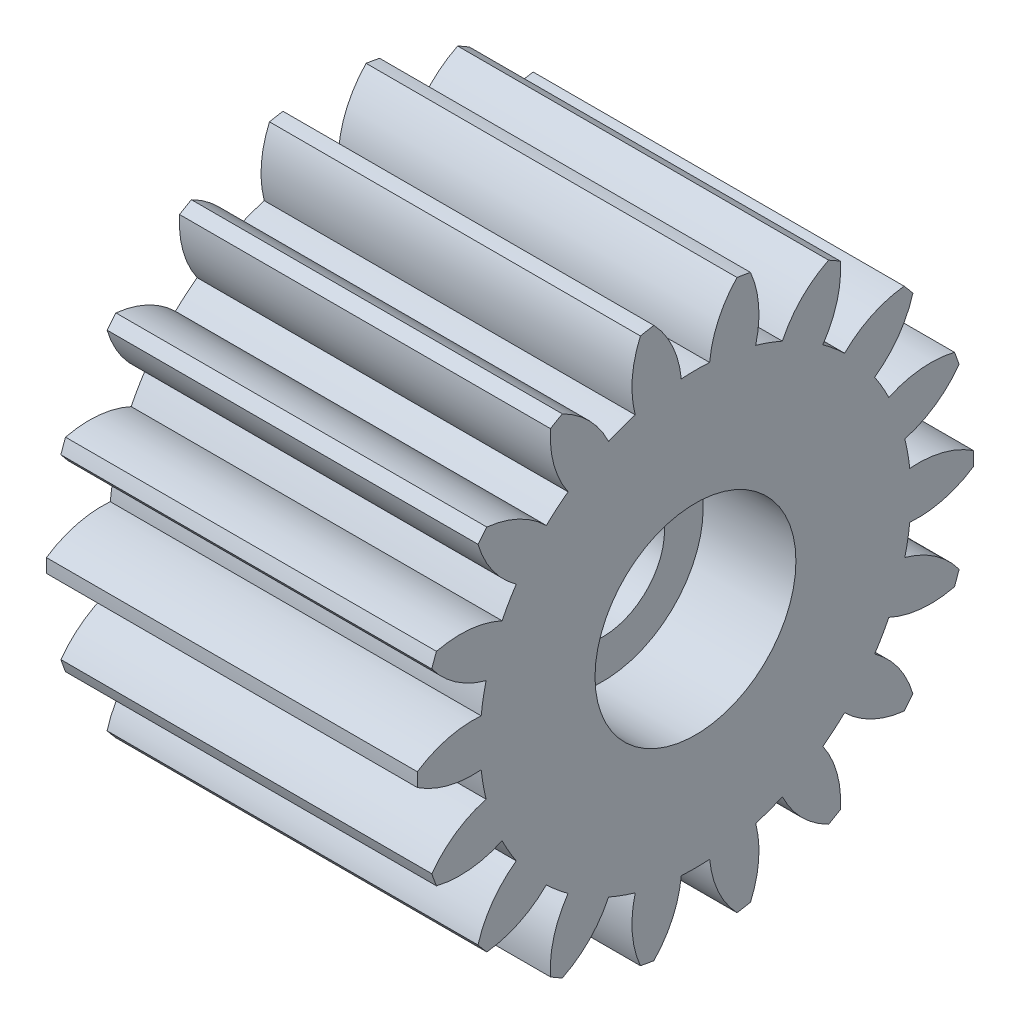
SolidWorks part; units mm, degrees
ref_plane "Plane1" through (0, 0, 0) normal (0, 0, 1) x (1, 0, 0)
ref_plane "Plane2" through (0, 0, 0) normal (0, 1, 0) x (1, 0, 0)
ref_plane "Plane3" through (0, 0, 0) normal (1, 0, 0) x (0, 0, -1)
other "Configuration Table"
sketch "HoldingSke" plane through (0, 0, 0) normal (0, 1, 0) x (1, 0, 0)
  line L0 (0, 0) -> (1.0567, -0.3434)
  line L1 (-15, 0) -> (100, 0) construction
  line L2 (0, 0) -> (-2.1039, 2.3779)
  line L3 (0, 0) -> (-11.863, 4.5341)
  line L4 (0, 0) -> (8.2133, 2.6687)
  line L5 (0, 0) -> (-46.8476, -17.4728)
  line L6 (0, 0) -> (-9.9476, -6.7116)
  line L7 (-2.1039, 2.3779) -> (8.6586, 51.2059)
  line L8 (-76.2, 54.61) -> (-75.2, 54.61)
  line L9 (-71.009, 38.7566) -> (-53.1078, 45.2721)
  line L10 (-76.2, 71.12) -> (104.1128, 71.12)
  line L11 (0, 0) -> (-12, 0)
  line L12 (-76.2, 101.6) -> (-76.166, 101.6)
  line L13 (24.9733, 27.94) -> (52.9518, 28.4284)
  line L14 (24.9733, 27.94) -> (24.9743, 27.94)
  line L15 (24.9733, 27.94) -> (100.4006, 29.5858)
  line L16 (-63.627, -0.9) -> (-12.827, -0.9)
  circle A0 centre (0, 0) radius 3
  circle A1 centre (0, 0) radius 6.974
  circle A2 centre (0, 0) radius 37.5
  circle A3 centre (0, 0) radius 3
  dimension "MHD" = 13.948
  dimension "Hub_dia" = 75
  dimension "Bore" = 6
  dimension "MBD" = 6
  dimension "Num_teeth" = 18
  dimension "Pitch" = 1.1111
  dimension "Overall_len" = 50
  dimension "Show_teeth" = 18
  dimension "Thickness" = 12
  dimension "OAL" = 50.0001
  dimension "T_dim" = 1
  dimension "Ap" = 20
  dimension "H" = 19.05
  dimension "Pitch_radius" = 180.3128
  dimension "Width" = 12
  dimension "Backlash" = 0.034
  dimension "Addendum_fac" = 1
  dimension "Dedendum_fac" = 1.25
  dimension "Clearance_fac" = 0.25
  dimension "Dedendum_add" = 0.001
  dimension "Module" = 0.9
sketch "BasProSke" plane through (0, 0, 0) normal (0, 1, 0) x (1, 0, 0)
  line L0 (-10, 0) -> (60, 0) construction
  line L1 (0, 0) -> (0, 9)
  line L2 (0, 0) -> (12, 0)
  line L3 (12, 0) -> (12, 9)
  line L4 (12, 9) -> (0, 9)
  dimension "Thickness" = 12
  dimension "Diameter" = 18
revolve "Base-Revolve" add sketch "BasProSke" angle 360 about L0
sketch "TooCutSke" plane through (0, 0, 0) normal (1, 0, 0) x (0, 0, -1)
  line L1 (0, 0) -> (0, 107) construction
  line L2 (0, 0) -> (-0.7654, 8.0638) construction
  line L3 (0, 0) -> (-2.8041, 15.903) construction
  line L4 (-0.7654, 8.0638) -> (-1.4021, 7.9515) construction
  arc A0 (0.4593, 6.9589) -> (-0.4593, 6.9589) centre (0, 0) ccw
  arc A1 (1.3655, 8.9215) -> (-1.3655, 8.9215) centre (0, 0) ccw
  circle A2 centre (0, 0) radius 8.1 construction
  circle A3 centre (0, 0) radius 7.6115 construction
  arc A4 (-0.4593, 6.9589) -> (-1.3655, 8.9215) centre (-3.6854, 6.6598) ccw
  arc A5 (1.3655, 8.9215) -> (0.4593, 6.9589) centre (3.6854, 6.6598) ccw
  dimension "Root_dia" = 13.948
  dimension "Overcut_dia" = 18.0508
  dimension "Pitch_dia" = 16.2
  dimension "Base_dia" = 15.223
  dimension "Flank_rad" = 3.24
  dimension "Half_ang" = 10
  dimension "Half_CT" = 0.6465
extrude "ToothCut" cut sketch "TooCutSke" along normal through all
fillet "Breaks" [suppressed] radius 0.018
fillet "RootFillets" [suppressed] radius 0.226
pattern_circular "TeethCuts" count 18 every 20 about axis through (-10, 0, 0) along (1, 0, 0) of "ToothCut", "RootFillets", "Breaks"
sketch "HubNeaOneSke" plane through (0, 0, 0) normal (-1, 0, 0) x (0, 0, 1)
  circle A0 centre (0, 0) radius 6.974
  dimension "Diameter" = 13.948
extrude "HubNearOne" [suppressed] add sketch "HubNeaOneSke" along normal blind 38.0001
sketch "HubNeaBotSke" plane through (0, 0, 0) normal (-1, 0, 0) x (0, 0, 1)
  circle A0 centre (0, 0) radius 6.974
  dimension "Diameter" = 13.948
extrude "HubNearBoth" [suppressed] add sketch "HubNeaBotSke" along normal blind 19
ref_plane "FarPln" through (12, 0, 0) normal (1, 0, 0) x (0, 0, -1)
sketch "HubFarSke" plane through (12, 0, 0) normal (1, 0, 0) x (0, 0, -1)
  circle A0 centre (0, 0) radius 6.974
  dimension "Diameter" = 13.948
extrude "HubFar" [suppressed] add sketch "HubFarSke" along normal blind 19
sketch "BorSke" plane through (0, 0, 0) normal (1, 0, 0) x (0, 0, -1)
  circle A0 centre (0, 0) radius 2
  dimension "Diameter" = 4
extrude "Bore" cut sketch "BorSke" along normal mid plane 100.0001
sketch "KeySke" plane through (0, 0, 0) normal (1, 0, 0) x (0, 0, -1)
  line L0 (-1, 0) -> (-1, 4)
  line L1 (-1, 4) -> (1, 4)
  line L2 (1, 4) -> (1, 0)
  line L3 (0, 0) -> (0, 34) construction
  line L4 (-1, 0) -> (1, 0)
  dimension "Offset" = 4
  dimension "Width" = 2
extrude "Keyway" [suppressed] cut sketch "KeySke" along normal mid plane 100.0001
pattern_circular "Keyway2" [suppressed] count 2 every 90 about axis through (-10, 0, 0) along (1, 0, 0)
sketch "Sketch2" plane through (12, 0, 0) normal (1, 0, 0) x (0, 0, -1)
  circle A0 centre (0, 0) radius 3.25
  dimension "D1" = 6.5
extrude "Cut-Extrude1" cut sketch "Sketch2" against normal blind 3
sketch "Sketch3" plane through (0, 0, 0) normal (-1, 0, 0) x (0, 0, 1)
  circle A0 centre (0, 0) radius 4.95
  dimension "D1" = 9.9
extrude "Cut-Extrude2" cut sketch "Sketch3" against normal blind 4
equation "' \"Module@HoldingSke\" = 6.35"
equation "' \"Num_teeth@HoldingSke\" = 12"
equation "' \"Ap@HoldingSke\" =  20"
equation "' \"Ap@HoldingSke\" = 20"
equation "' \"Width@HoldingSke\" = 0.5 * 25.4"
equation "' \"Hub_dia@HoldingSke\"= 1 * 25.4"
equation "' \"Hub_dia@HoldingSke\" = 1 * 25.4"
equation "' \"Overall_len@HoldingSke\" = 1.0 * 25.4"
equation "' \"Bore@HoldingSke\" = 0.75 * 25.4"
equation "' \"T_dim@HoldingSke\" = 0.1 * 25.4"
equation "' \"Width@KeySke\" = 0.25 * 25.4"
equation "' \"Show_teeth@HoldingSke\" = 13"
equation "' \"Backlash@HoldingSke\" = 0.009 * 25.4"
equation "' \"Addendum_fac@HoldingSke\" = 1.0"
equation "' \"Dedendum_fac@HoldingSke\" = 1.25"
equation "' \"Dedendum_add@HoldingSke\" = 0.00005 * 25.4"
equation "' \"Clearance_fac@HoldingSke\" = 0.25"
equation "\"Pitch@HoldingSke\" = 1 / \"Module@HoldingSke\""
equation "\"Overcut_dia@TooCutSke\" = (\"Num_teeth@HoldingSke\" + 2 * \"Addendum_fac@HoldingSke\") / \"Pitch@HoldingSke\" + 0.002 * 25.4"
equation "\"Pitch_dia@TooCutSke\" = \"Num_teeth@HoldingSke\" / \"Pitch@HoldingSke\""
equation "\"Base_dia@TooCutSke\" = \"Num_teeth@HoldingSke\" / \"Pitch@HoldingSke\" * cos((\"Ap@HoldingSke\"  * 3.14159265 / 180))"
equation "\"Root_dia@TooCutSke\" = (\"Num_teeth@HoldingSke\" + 2) / \"Pitch@HoldingSke\" - 2 * (\"Addendum_fac@HoldingSke\" + \"Dedendum_fac@HoldingSke\") / \"Pitch@HoldingSke\" - \"Dedendum_add@HoldingSke\" * 2"
equation "\"Half_ang@TooCutSke\" = 180 / \"Num_teeth@HoldingSke\""
equation "\"Half_CT@TooCutSke\" = \"Num_teeth@HoldingSke\" / \"Pitch@HoldingSke\" * sin((3.14159265 / 2 / \"Num_teeth@HoldingSke\")) / 2 - 7 * \"Backlash@HoldingSke\" / 4"
equation "\"Flank_rad@TooCutSke\" = \"Num_teeth@HoldingSke\" / \"Pitch@HoldingSke\" / 5"
equation "\"Radius@RootFillets\" = \"Clearance_fac@HoldingSke\" / \"Pitch@HoldingSke\" + \"Dedendum_add@HoldingSke\""
equation "\"Break_rad@Breaks\" = 0.02 / \"Pitch@HoldingSke\""
equation "\"Thickness@HoldingSke\" = \"Width@HoldingSke\""
equation "\"OAL@HoldingSke\" = \"Thickness@HoldingSke\""
equation "\"MHD@HoldingSke\" = (\"Num_teeth@HoldingSke\" + 2) / \"Pitch@HoldingSke\" - 2 * (\"Addendum_fac@HoldingSke\" + \"Dedendum_fac@HoldingSke\")  / \"Pitch@HoldingSke\" - \"Dedendum_add@HoldingSke\" * 2"
equation "\"MBD@HoldingSke\" = (\"Num_teeth@HoldingSke\" + 2) / \"Pitch@HoldingSke\" - 2 * (\"Addendum_fac@HoldingSke\" + \"Dedendum_fac@HoldingSke\")  / \"Pitch@HoldingSke\" - \"Dedendum_add@HoldingSke\" * 2 - 0.002 * 25.4"
equation "\"MHD@HoldingSke\" = ((sgn( \"MHD@HoldingSke\" - \"Hub_dia@HoldingSke\" )-1)*( \"MHD@HoldingSke\" - \"Hub_dia@HoldingSke\" ))/-2+ \"Hub_dia@HoldingSke\""
equation "\"MBD@HoldingSke\" = ((sgn( \"MBD@HoldingSke\" - \"Bore@HoldingSke\" )-1)*( \"MBD@HoldingSke\" - \"Bore@HoldingSke\" ))/-2+ \"Bore@HoldingSke\""
equation "\"OAL@HoldingSke\" = ((sgn( \"OAL@HoldingSke\" - \"Overall_len@HoldingSke\" )+1)*( \"OAL@HoldingSke\" - \"Overall_len@HoldingSke\" ))/2 + \"Overall_len@HoldingSke\" + 0.000002 * 25.4"
equation "\"Num_teeth@TeethCuts\" = int( \"Show_teeth@HoldingSke\" ) + 1"
equation "\"Num_teeth@TeethCuts\" = ((sgn( \"Num_teeth@TeethCuts\" - \"Num_teeth@HoldingSke\" )-1)*( \"Num_teeth@TeethCuts\" - \"Num_teeth@HoldingSke\" ))/-2+ \"Num_teeth@HoldingSke\""
equation "\"Num_teeth@TeethCuts\" = ((sgn( \"Num_teeth@TeethCuts\" - 2.0)+1)*( \"Num_teeth@TeethCuts\" - 2.0))/2 +2.0"
equation "\"Angle@TeethCuts\" = 360.0 / \"Num_teeth@HoldingSke\""
equation "\"Diameter@BasProSke\" = (\"Num_teeth@HoldingSke\" + 2 * \"Addendum_fac@HoldingSke\") / \"Pitch@HoldingSke\""
equation "\"Thickness@BasProSke\"  = \"Thickness@HoldingSke\""
equation "' \"Fillet_rad@BasProSke\" =  \"Thickness@HoldingSke\" * 0.05"
equation "' \"Fillet_rad@BasProSke\" = \"Thickness@HoldingSke\" * 0.05"
equation "\"MHD@HoldingSke\" = ((sgn( \"MHD@HoldingSke\" - \"Root_dia@TooCutSke\" )-1)*( \"MHD@HoldingSke\" - \"Root_dia@TooCutSke\" ))/-2+ \"Root_dia@TooCutSke\""
equation "\"Diameter@HubNeaOneSke\" = \"MHD@HoldingSke\""
equation "\"Length@HubNearOne\" = \"OAL@HoldingSke\" - \"Thickness@BasProSke\""
equation "\"Diameter@HubNeaBotSke\" = \"MHD@HoldingSke\""
equation "\"Length@HubNearBoth\" = ( \"OAL@HoldingSke\" - \"Thickness@BasProSke\" ) / 2.0"
equation "\"Thickness@FarPln\" = \"Thickness@BasProSke\""
equation "\"Diameter@HubFarSke\" = \"MHD@HoldingSke\""
equation "\"Length@HubFar\" = ( \"OAL@HoldingSke\" - \"Thickness@BasProSke\" ) / 2.0"
equation "\"D1@Bore\" = \"OAL@HoldingSke\" * 2.0"
equation "\"D1@Keyway\" = \"OAL@HoldingSke\" * 2.0"
equation "\"Offset@KeySke\" = \"T_dim@HoldingSke\" + \"MBD@HoldingSke\" / 2.0"
